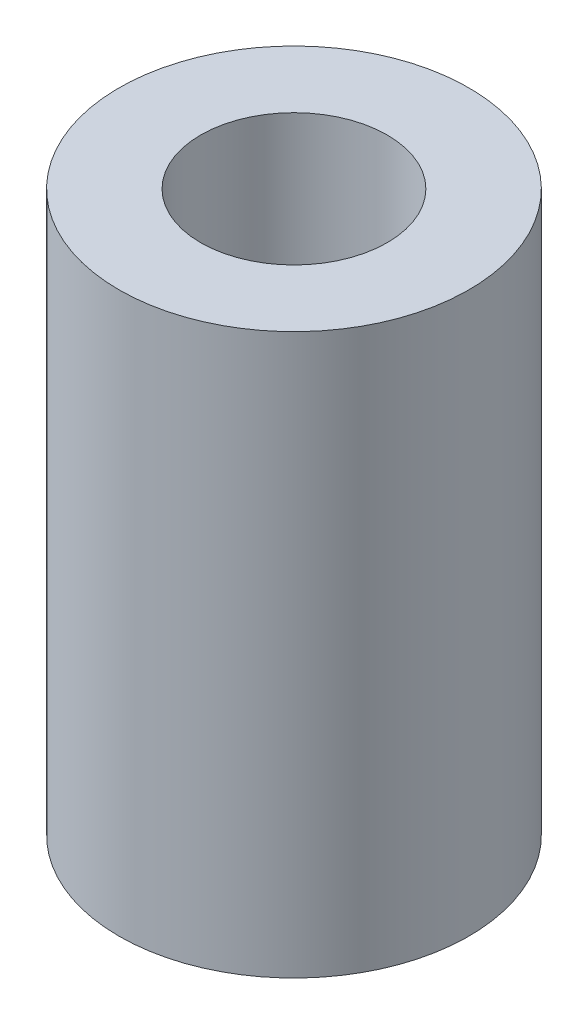
SolidWorks part; units mm, degrees
ref_plane "Front Plane" through (0, 0, 0) normal (0, 0, 1) x (1, 0, 0)
ref_plane "Top Plane" through (0, 0, 0) normal (0, 1, 0) x (1, 0, 0)
ref_plane "Right Plane" through (0, 0, 0) normal (1, 0, 0) x (0, 0, -1)
sketch "Sketch1" plane through (0, 0, 0) normal (0, 1, 0) x (1, 0, 0)
  circle A0 centre (0, 0) radius 7.5
  circle A1 centre (0, 0) radius 4
  dimension "D1" = 8
  dimension "D2" = 15
extrude "Boss-Extrude1" add sketch "Sketch1" along normal blind 24
equation "\"shaft_diam\"=0.314961"
equation "\"D1@Sketch1\"=\"shaft_diam\""
equation "\"linear_bearing_od\"=0.590551"
equation "\"D2@Sketch1\"=\"linear_bearing_od\""
equation "\"linear_bearing_len\"=0.944882"
equation "\"D1@Boss-Extrude1\"=\"linear_bearing_len\""
